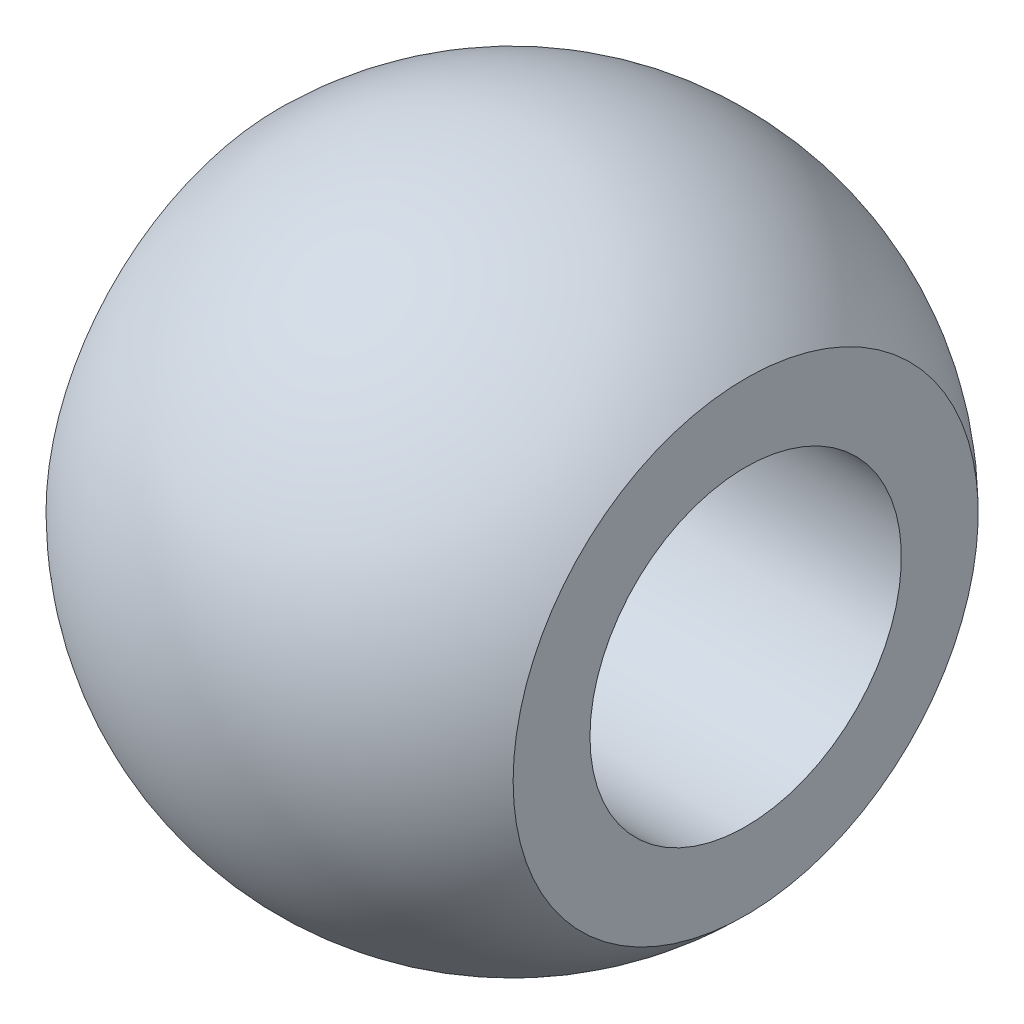
SolidWorks part; units mm, degrees
material "Alloy Steel"
ref_plane "Front Plane" through (0, 0, 0) normal (0, 0, 1) x (1, 0, 0)
ref_plane "Top Plane" through (0, 0, 0) normal (0, 1, 0) x (1, 0, 0)
ref_plane "Right Plane" through (0, 0, 0) normal (1, 0, 0) x (0, 0, -1)
sketch "Sketch1" plane through (0, 0, 0) normal (0, 0, 1) x (1, 0, 0)
  line L1 (-4.5, 3) -> (4.5, 3)
  line L2 (0, 0) -> (2.388, 0)
  line L5 (4.5, 3) -> (4.5, 4.4802)
  line L6 (-4.5, 3) -> (-4.5, 4.4802)
  arc A0 (4.5, 4.4802) -> (-4.5, 4.4802) centre (0, 0) ccw
  point P1 (0, 3)
  dimension "D2" = 3
  dimension "D4" = 6.35
  dimension "D1" = 9
revolve "Revolve1" add sketch "Sketch1" angle 360 about L2
sketch "Sketch2" plane through (0, 0, 0) normal (0, 0, 1) x (1, 0, 0)
  point P0 (0, 0)
